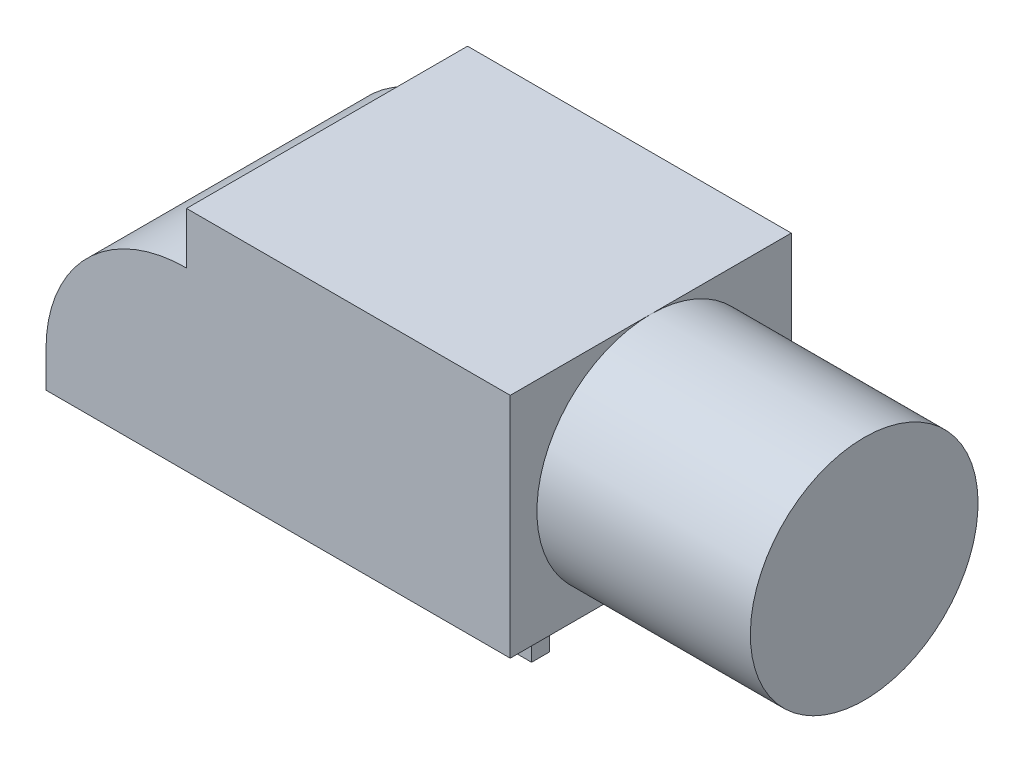
SolidWorks part; units mm, degrees
ref_plane "Front Plane" through (0, 0, 0) normal (0, 0, 1) x (1, 0, 0)
ref_plane "Top Plane" through (0, 0, 0) normal (0, 1, 0) x (1, 0, 0)
ref_plane "Right Plane" through (0, 0, 0) normal (1, 0, 0) x (0, 0, -1)
sketch "Sketch1" plane through (0, 0, 0) normal (0, 0, 1) x (1, 0, 0)
  line L1 (-9.525, 3.2) -> (9.525, 3.2)
  line L2 (-9.525, 3.2) -> (-9.525, -3.2)
  line L3 (-9.525, -3.2) -> (9.525, -3.2)
  line L4 (9.525, 3.2) -> (9.525, -3.2)
  line L5 (-9.525, 3.2) -> (9.525, -3.2) construction
  line L6 (-9.525, -3.2) -> (9.525, 3.2) construction
  point P0 (0, 0)
  dimension "D1" = 6.4
  dimension "D2" = 19.05
extrude "Boss-Extrude1" add sketch "Sketch1" along normal mid plane 7.9
sketch "Sketch2" plane through (9.525, 0, 0) normal (1, 0, 0) x (0, 0, -1)
  line L0 (-3.95, 3.2) -> (3.95, 3.2) construction
  circle A0 centre (0, 0) radius 3.2
extrude "Cut-Extrude1" cut sketch "Sketch2" against normal blind 6 flip side to cut
sketch "Sketch3" plane through (0, -3.2, 0) normal (0, -1, 0) x (1, 0, 0)
  line L0 (2.325, 2.5) -> (2.325, -2.5) construction
  line L1 (1.725, 2.75) -> (2.925, 2.75)
  line L2 (1.725, 2.75) -> (1.725, 2.25)
  line L3 (1.725, 2.25) -> (2.925, 2.25)
  line L4 (2.925, 2.75) -> (2.925, 2.25)
  line L5 (1.725, 2.75) -> (2.925, 2.25) construction
  line L6 (1.725, 2.25) -> (2.925, 2.75) construction
  line L7 (1.725, -2.25) -> (2.925, -2.25)
  line L8 (1.725, -2.25) -> (1.725, -2.75)
  line L9 (1.725, -2.75) -> (2.925, -2.75)
  line L10 (2.925, -2.25) -> (2.925, -2.75)
  line L11 (1.725, -2.25) -> (2.925, -2.75) construction
  line L12 (1.725, -2.75) -> (2.925, -2.25) construction
  line L13 (9.525, -3.2) -> (9.525, 3.2) construction
  line L14 (0, 0) -> (2.325, 0) construction
  circle A0 centre (-7.875, 0) radius 0.75
  point P0 (2.325, 2.5)
  point P5 (2.325, -2.5)
  dimension "D4" = 17.4
  dimension "D5" = 1.5
  dimension "D1" = 1.2
  dimension "D2" = 0.5
  dimension "D3" = 10.2
  dimension "D6" = 5
extrude "Boss-Extrude2" add sketch "Sketch3" along normal blind 1
sketch "Sketch4" plane through (0, 0, 3.95) normal (0, 0, 1) x (1, 0, 0)
  line L0 (-9.4949, -3.2002) -> (9.5547, -3.0672) construction
  dimension "D1" = 19.05
sketch "Sketch5" plane through (0, 0, 3.95) normal (0, 0, 1) x (1, 0, 0)
  line L0 (-5.575, 3.2) -> (-5.575, 1.75)
  line L1 (3.525, 3.2) -> (-9.525, 3.2) construction
  line L2 (-9.525, 3.2) -> (-9.525, -3.2) construction
  line L3 (-9.525, -2.2) -> (-9.525, -3.2)
  arc A0 (-5.575, 1.75) -> (-9.525, -2.2) centre (-5.575, -2.2) ccw
  dimension "D1" = 3.95
  dimension "D2" = 1
extrude "Cut-Extrude2" cut sketch "Sketch5" against normal through all and the other way through all flip side to cut
